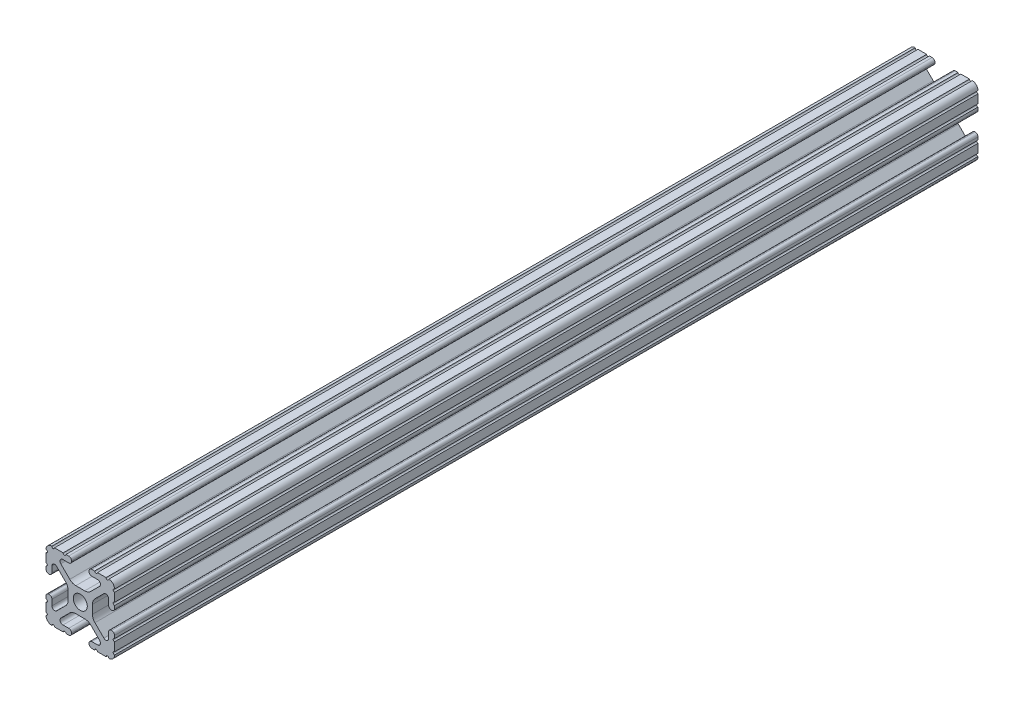
SolidWorks part; units mm, degrees
ref_plane "Front Plane" through (0, 0, 0) normal (0, 0, 1) x (1, 0, 0)
ref_plane "Top Plane" through (0, 0, 0) normal (0, 1, 0) x (1, 0, 0)
ref_plane "Right Plane" through (0, 0, 0) normal (1, 0, 0) x (0, 0, -1)
sketch "Sketch1" plane through (0, 0, 0) normal (0, 0, 1) x (1, 0, 0)
  line L0 (-7.207, 8.7244) -> (-3.8983, 5.4232)
  line L1 (-4.2875, 10.4902) -> (-6.4768, 10.4902)
  line L2 (-3.2385, 11.651) -> (-3.2385, 11.5392)
  line L3 (-5.3171, 12.7) -> (-4.2875, 12.7)
  line L4 (0, 13.4005) -> (0, -14.8534) construction
  line L5 (12.7, 0) -> (-13.9989, 0) construction
  line L6 (-9.5504, 12.7) -> (-6.3331, 12.7)
  line L7 (-12.7, 6.3331) -> (-12.7, 9.5504)
  line L8 (-12.7, 4.2875) -> (-12.7, 5.3171)
  line L9 (-11.5392, 3.2385) -> (-11.651, 3.2385)
  line L10 (-10.4902, 6.4021) -> (-10.4902, 4.2875)
  line L11 (-5.441, 3.8408) -> (-8.7371, 7.1294)
  line L12 (-4.5085, -1.5932) -> (-4.5085, 1.5932)
  line L13 (-1.7093, -4.4958) -> (1.7093, -4.4958)
  line L14 (3.9523, -5.4237) -> (7.1797, -8.6452)
  line L15 (6.4164, -10.4902) -> (4.2875, -10.4902)
  line L16 (3.2385, -11.5392) -> (3.2385, -11.651)
  line L17 (4.2875, -12.7) -> (5.3171, -12.7)
  line L18 (6.3331, -12.7) -> (9.5504, -12.7)
  line L19 (12.7, -9.5504) -> (12.7, -6.3331)
  line L20 (12.7, -5.3171) -> (12.7, -4.2875)
  line L21 (11.651, -3.2385) -> (11.5392, -3.2385)
  line L22 (10.4902, -4.2875) -> (10.4902, -6.4021)
  line L23 (8.7371, -7.1294) -> (5.441, -3.8408)
  line L24 (4.5085, -1.5932) -> (4.5085, 1.5932)
  line L25 (5.441, 3.8408) -> (8.7371, 7.1294)
  line L26 (10.4902, 6.4021) -> (10.4902, 4.2875)
  line L27 (11.5392, 3.2385) -> (11.651, 3.2385)
  line L28 (12.7, 4.2875) -> (12.7, 5.3171)
  line L29 (12.7, 6.3331) -> (12.7, 9.5504)
  line L30 (9.5504, 12.7) -> (6.3331, 12.7)
  line L31 (5.3171, 12.7) -> (4.2875, 12.7)
  line L32 (3.2385, 11.651) -> (3.2385, 11.5392)
  line L33 (4.2875, 10.4902) -> (6.4768, 10.4902)
  line L34 (7.207, 8.7244) -> (3.8983, 5.4232)
  line L35 (1.6558, 4.4958) -> (-1.6558, 4.4958)
  line L36 (-8.7371, -7.1294) -> (-5.441, -3.8408)
  line L37 (-10.4902, -4.2875) -> (-10.4902, -6.4021)
  line L38 (-11.651, -3.2385) -> (-11.5392, -3.2385)
  line L39 (-12.7, -5.3171) -> (-12.7, -4.2875)
  line L40 (-12.7, -9.5504) -> (-12.7, -6.3331)
  line L41 (-6.3331, -12.7) -> (-9.5504, -12.7)
  line L42 (-4.2875, -12.7) -> (-5.3171, -12.7)
  line L43 (-3.2385, -11.5392) -> (-3.2385, -11.651)
  line L44 (-6.4164, -10.4902) -> (-4.2875, -10.4902)
  line L45 (-3.9523, -5.4237) -> (-7.1797, -8.6452)
  arc A0 (-7.207, 8.7244) -> (-6.4768, 10.4902) centre (-6.4768, 9.4563) cw
  arc A1 (-3.2385, 11.5392) -> (-4.2875, 10.4902) centre (-4.2875, 11.5392) cw
  arc A2 (-4.2875, 12.7) -> (-3.2385, 11.651) centre (-4.2875, 11.651) cw
  arc A3 (-5.3171, 12.7) -> (-6.3331, 12.7) centre (-5.8251, 12.7) cw
  arc A4 (-9.5504, 12.7) -> (-10.5664, 12.6998) centre (-10.0584, 12.7) cw
  arc A5 (-12.6998, 10.5664) -> (-10.5664, 12.6998) centre (-10.5918, 10.5918) cw
  arc A6 (-12.6998, 10.5664) -> (-12.7, 9.5504) centre (-12.7, 10.0584) cw
  arc A7 (-12.7, 6.3331) -> (-12.7, 5.3171) centre (-12.7, 5.8251) cw
  arc A8 (-11.651, 3.2385) -> (-12.7, 4.2875) centre (-11.651, 4.2875) cw
  arc A9 (-10.4902, 4.2875) -> (-11.5392, 3.2385) centre (-11.5392, 4.2875) cw
  circle A10 centre (0, 0) radius 2.6035
  arc A11 (-10.4902, 6.4021) -> (-8.7371, 7.1294) centre (-9.4628, 6.4021) cw
  arc A12 (-5.441, 3.8408) -> (-4.5085, 1.5932) centre (-7.6835, 1.5932) cw
  arc A13 (-4.5085, -1.5932) -> (-5.441, -3.8408) centre (-7.6835, -1.5932) cw
  arc A14 (-8.7371, -7.1294) -> (-10.4902, -6.4021) centre (-9.4628, -6.4021) cw
  arc A15 (-1.7093, -4.4958) -> (-3.9523, -5.4237) centre (-1.7093, -7.6708) ccw
  arc A16 (3.9523, -5.4237) -> (1.7093, -4.4958) centre (1.7093, -7.6708) ccw
  arc A17 (6.4164, -10.4902) -> (7.1797, -8.6452) centre (6.4164, -9.4098) ccw
  arc A18 (4.2875, -10.4902) -> (3.2385, -11.5392) centre (4.2875, -11.5392) ccw
  arc A19 (3.2385, -11.651) -> (4.2875, -12.7) centre (4.2875, -11.651) ccw
  arc A20 (6.3331, -12.7) -> (5.3171, -12.7) centre (5.8251, -12.7) ccw
  arc A21 (10.5664, -12.6998) -> (9.5504, -12.7) centre (10.0584, -12.7) ccw
  arc A22 (10.5664, -12.6998) -> (12.6998, -10.5664) centre (10.5918, -10.5918) ccw
  arc A23 (12.7, -9.5504) -> (12.6998, -10.5664) centre (12.7, -10.0584) ccw
  arc A24 (12.7, -5.3171) -> (12.7, -6.3331) centre (12.7, -5.8251) ccw
  arc A25 (12.7, -4.2875) -> (11.651, -3.2385) centre (11.651, -4.2875) ccw
  arc A26 (11.5392, -3.2385) -> (10.4902, -4.2875) centre (11.5392, -4.2875) ccw
  arc A27 (8.7371, -7.1294) -> (10.4902, -6.4021) centre (9.4628, -6.4021) ccw
  arc A28 (4.5085, -1.5932) -> (5.441, -3.8408) centre (7.6835, -1.5932) ccw
  arc A29 (5.441, 3.8408) -> (4.5085, 1.5932) centre (7.6835, 1.5932) ccw
  arc A30 (10.4902, 6.4021) -> (8.7371, 7.1294) centre (9.4628, 6.4021) ccw
  arc A31 (10.4902, 4.2875) -> (11.5392, 3.2385) centre (11.5392, 4.2875) ccw
  arc A32 (11.651, 3.2385) -> (12.7, 4.2875) centre (11.651, 4.2875) ccw
  arc A33 (12.7, 6.3331) -> (12.7, 5.3171) centre (12.7, 5.8251) ccw
  arc A34 (12.6998, 10.5664) -> (12.7, 9.5504) centre (12.7, 10.0584) ccw
  arc A35 (12.6998, 10.5664) -> (10.5664, 12.6998) centre (10.5918, 10.5918) ccw
  arc A36 (9.5504, 12.7) -> (10.5664, 12.6998) centre (10.0584, 12.7) ccw
  arc A37 (5.3171, 12.7) -> (6.3331, 12.7) centre (5.8251, 12.7) ccw
  arc A38 (4.2875, 12.7) -> (3.2385, 11.651) centre (4.2875, 11.651) ccw
  arc A39 (3.2385, 11.5392) -> (4.2875, 10.4902) centre (4.2875, 11.5392) ccw
  arc A40 (7.207, 8.7244) -> (6.4768, 10.4902) centre (6.4768, 9.4563) ccw
  arc A41 (1.6558, 4.4958) -> (3.8983, 5.4232) centre (1.6558, 7.6708) ccw
  arc A42 (-1.6558, 4.4958) -> (-3.8983, 5.4232) centre (-1.6558, 7.6708) cw
  arc A43 (-11.5392, -3.2385) -> (-10.4902, -4.2875) centre (-11.5392, -4.2875) cw
  arc A44 (-12.7, -4.2875) -> (-11.651, -3.2385) centre (-11.651, -4.2875) cw
  arc A45 (-12.7, -5.3171) -> (-12.7, -6.3331) centre (-12.7, -5.8251) cw
  arc A46 (-12.7, -9.5504) -> (-12.6998, -10.5664) centre (-12.7, -10.0584) cw
  arc A47 (-10.5664, -12.6998) -> (-12.6998, -10.5664) centre (-10.5918, -10.5918) cw
  arc A48 (-10.5664, -12.6998) -> (-9.5504, -12.7) centre (-10.0584, -12.7) cw
  arc A49 (-6.3331, -12.7) -> (-5.3171, -12.7) centre (-5.8251, -12.7) cw
  arc A50 (-3.2385, -11.651) -> (-4.2875, -12.7) centre (-4.2875, -11.651) cw
  arc A51 (-4.2875, -10.4902) -> (-3.2385, -11.5392) centre (-4.2875, -11.5392) cw
  arc A52 (-6.4164, -10.4902) -> (-7.1797, -8.6452) centre (-6.4164, -9.4098) cw
  dimension "D1" = 5.207
  dimension "D9" = 14.859
  dimension "D2" = 25.4
  dimension "D3" = 12.7
  dimension "D4" = 6.477
  dimension "D5" = 8.2042
  dimension "D6" = 9.017
  dimension "D8" = 2.2098
  dimension "D10" = 2.2098
extrude "Extrude1" add sketch "Sketch1" against normal blind 320
